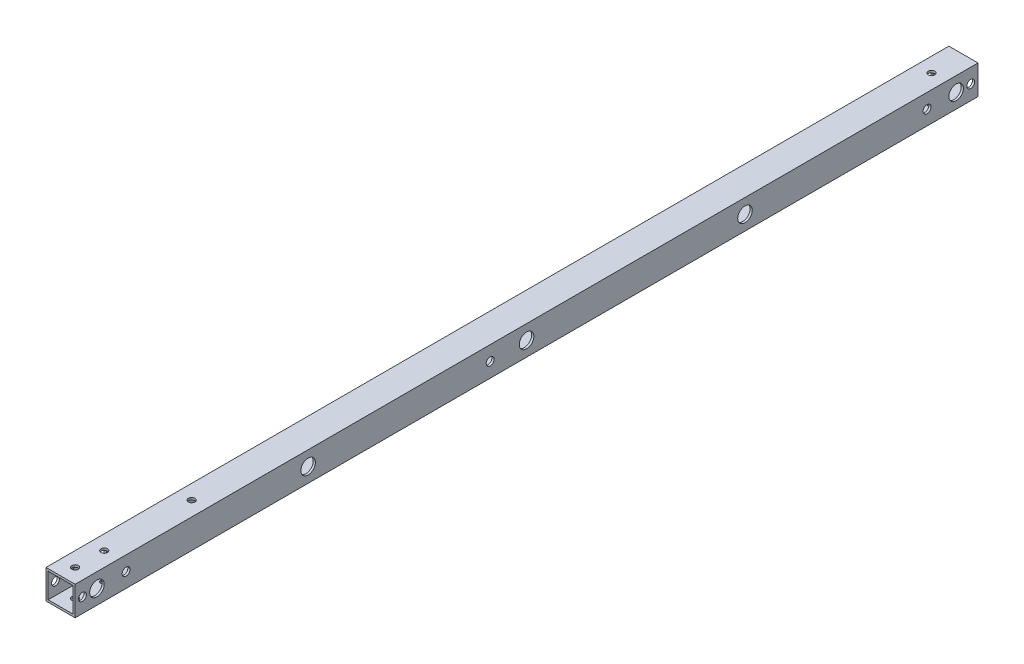
SolidWorks part; units mm, degrees
material "6063-T5"
ref_plane "正面" through (0, 0, 0) normal (0, 0, 1) x (1, 0, 0)
ref_plane "平面" through (0, 0, 0) normal (0, 1, 0) x (1, 0, 0)
ref_plane "右側面" through (0, 0, 0) normal (1, 0, 0) x (0, 0, -1)
sketch "ｽｹｯﾁ1" plane through (0, 0, 0) normal (0, 0, 1) x (1, 0, 0)
  line L1 (-10, -10) -> (10, -10)
  line L2 (-10, -10) -> (-10, 10)
  line L3 (-10, 10) -> (10, 10)
  line L4 (10, -10) -> (10, 10)
  line L5 (-10, -10) -> (10, 10) construction
  line L6 (-10, 10) -> (10, -10) construction
  line L7 (-8.5, -8.5) -> (8.5, -8.5)
  line L8 (-8.5, -8.5) -> (-8.5, 8.5)
  line L9 (-8.5, 8.5) -> (8.5, 8.5)
  line L10 (8.5, -8.5) -> (8.5, 8.5)
  line L11 (-8.5, -8.5) -> (8.5, 8.5) construction
  line L12 (-8.5, 8.5) -> (8.5, -8.5) construction
  point P0 (0, 0)
  point P6 (0, 0)
  dimension "D1" = 1.5
  dimension "D2" = 20
  dimension "D3" = 20
extrude "ﾎﾞｽ - 押し出し1" add sketch "ｽｹｯﾁ1" along normal blind 620
sketch "ｽｹｯﾁ2" plane through (10, 0, 0) normal (1, 0, 0) x (0, 0, -1)
  line L0 (-620, -10) -> (0, -10) construction
  line L1 (-620, -10) -> (-620, 10) construction
  circle A4 centre (-585, 0) radius 2.7
  circle A9 centre (-35, 0) radius 2.7
  circle A14 centre (-335, 0) radius 2.7
  dimension "D1" = 5.4
  dimension "D2" = 550
  dimension "D3" = 10
  dimension "D6" = 2
  dimension "D7" = 250
  dimension "D4" = 2
  dimension "D5" = 35
extrude "ｶｯﾄ - 押し出し1" cut sketch "ｽｹｯﾁ2" against normal blind 25
sketch "ｽｹｯﾁ3" plane through (0, 10, 0) normal (0, 1, 0) x (1, 0, 0)
  line L2 (10, -620) -> (10, 0) construction
  line L3 (10, 0) -> (-10, 0) construction
  circle A1 centre (0, -22) radius 2.25
  circle A6 centre (0, -610) radius 2.25
  circle A7 centre (0, -530) radius 2.25
  circle A8 centre (0, -590) radius 2.25
  dimension "D2" = 22
  dimension "D3" = 4.5
  dimension "D7" = 80
  dimension "D8" = 2
  dimension "D9" = 10
  dimension "D11" = 10
  dimension "D4" = 10
  dimension "D5" = 4.5
  dimension "D10" = 20
  dimension "D6" = 2
extrude "ｶｯﾄ - 押し出し2" cut sketch "ｽｹｯﾁ3" against normal blind 25
sketch "ｽｹｯﾁ4" plane through (10, 0, 0) normal (1, 0, 0) x (0, 0, -1)
  line L0 (0, 8.5) -> (0, -8.5) construction
  line L1 (-620, 10) -> (0, 10) construction
  line L2 (0, -10) -> (0, 10) construction
  line L3 (-620, -10) -> (0, -10) construction
  line L4 (-620, -10) -> (-620, 10) construction
  circle A0 centre (-15, 0) radius 2.7
  circle A1 centre (-5, 0) radius 2.7
  circle A2 centre (-615, 0) radius 2.7
  circle A3 centre (-605, 0) radius 2.7
  dimension "D1" = 15
  dimension "D2" = 10
  dimension "D3" = 5.4
  dimension "D4" = 5.4
  dimension "D5" = 5.4
  dimension "D6" = 5
  dimension "D7" = 10
  dimension "D8" = 10
  dimension "D9" = 5
  dimension "D11" = 15
  dimension "D10" = 5.4
  dimension "D12" = 10
extrude "ｶｯﾄ - 押し出し3" cut sketch "ｽｹｯﾁ4" against normal blind 40
sketch "ｽｹｯﾁ6" plane through (0, -10, 0) normal (0, -1, 0) x (-1, 0, 0)
  circle A0 centre (0, -530) radius 5
  dimension "D1" = 10
extrude "ｶｯﾄ - 押し出し4" cut sketch "ｽｹｯﾁ6" against normal blind 10
sketch "ｽｹｯﾁ7" plane through (-10, 0, 0) normal (1, 0, 0) x (0, 0, -1)
  circle A0 centre (-585, 0) radius 5
  circle A1 centre (-335, 0) radius 5
  circle A2 centre (-35, 0) radius 5
  dimension "D1" = 10
  dimension "D2" = 10
  dimension "D3" = 10
extrude "ｶｯﾄ - 押し出し5" cut sketch "ｽｹｯﾁ7" along normal blind 10
sketch "ｽｹｯﾁ8" plane through (10, 0, 0) normal (1, 0, 0) x (0, 0, -1)
  circle A0 centre (-605, 0) radius 5
  circle A1 centre (-15, 0) radius 5
  dimension "D1" = 10
  dimension "D2" = 10
extrude "ｶｯﾄ - 押し出し6" cut sketch "ｽｹｯﾁ8" against normal blind 5
sketch "ｽｹｯﾁ9" plane through (-10, 0, 0) normal (1, 0, 0) x (0, 0, -1)
  line L0 (-620, 10) -> (-620, -10) construction
  point P0 (-460, 0)
  point P1 (-310, 0)
  point P2 (-160, 0)
  point P5 (0, 0)
  point P6 (-620, 0)
  point P9 (-663.3597, -207.5296)
  point P10 (-553.7846, -175.8373)
  point P13 (-644.5072, -250.1953)
  point P14 (-621.6652, -272.5756)
  dimension "D1" = 160
  dimension "D2" = 150
  dimension "D3" = 150
hole_wizard "Ø4.3 (4.3) 直径の穴1" positions "ｽｹｯﾁ9" profile "ｽｹｯﾁ10" hole size "Ø4.3" standard "JIS" end condition through all
sketch "ｽｹｯﾁ10" plane through (-10, 0, 460) normal (0, 1, 0) x (0, 0, 1)
  line L0 (0, 0) -> (0, 20)
  line L1 (0, 20) -> (2.15, 20)
  line L2 (2.15, 20) -> (2.15, 0)
  line L5 (2.15, 0) -> (0, 0)
  line L11 (0, -6.35) -> (0, 107.95) construction
  dimension "通し穴の直径" = 4.3
  dimension "通し穴の深さ" = 20
hole_wizard "Ø10.0 (10) 直径の穴1" positions "ｽｹｯﾁ11" profile "ｽｹｯﾁ13" hole size "Ø10.0" standard "JIS"
sketch "ｽｹｯﾁ11" plane through (10, 0, 0) normal (1, 0, 0) x (0, 0, -1)
  point P0 (-460, 0)
  point P3 (-310, 0)
  point P6 (-160, 0)
sketch "ｽｹｯﾁ13" plane through (10, 0, 460) normal (0, 1, 0) x (0, 0, -1)
  line L0 (0, 0) -> (0, 1.5)
  line L1 (0, 1.5) -> (5, 1.5)
  line L2 (5, 1.5) -> (5, 0)
  line L5 (5, 0) -> (0, 0)
  line L10 (0, 1.5) -> (-5, 1.5) construction
  line L11 (0, -6.35) -> (0, 107.95) construction
  dimension "穴の直径" = 10
  dimension "穴の深さ" = 1.5
  dimension "ﾄﾞﾘﾙ角度" = 180
